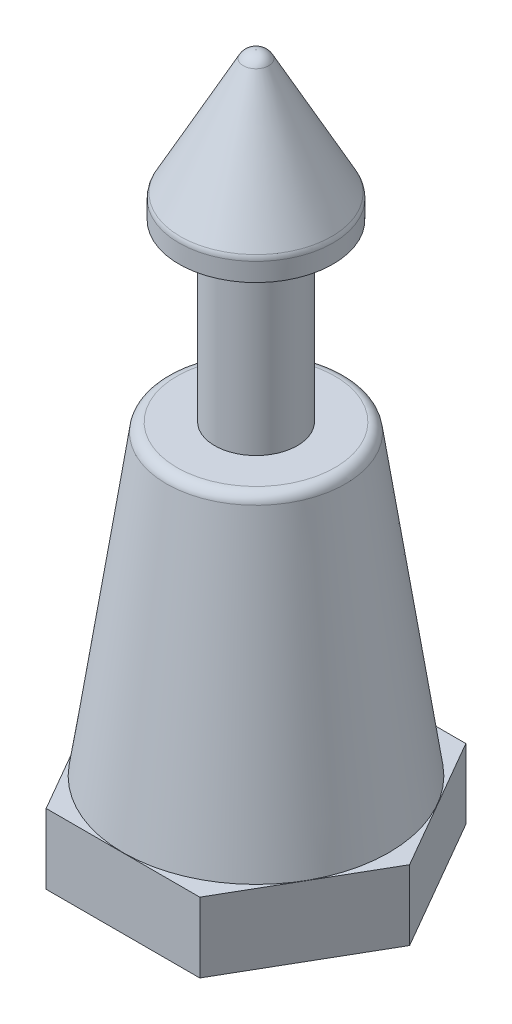
SolidWorks part; units mm, degrees
ref_plane "Front Plane" through (0, 0, 0) normal (0, 0, 1) x (1, 0, 0)
ref_plane "Top Plane" through (0, 0, 0) normal (0, 1, 0) x (1, 0, 0)
ref_plane "Right Plane" through (0, 0, 0) normal (1, 0, 0) x (0, 0, -1)
sketch "Sketch1" plane through (0, 0, 0) normal (0, 0, 1) x (1, 0, 0)
  line L0 (0, 0) -> (0, 79.052) construction
  line L1 (4.826, 2.4892) -> (4.826, 0)
  line L3 (0, 0) -> (4.826, 0)
  line L4 (4.826, 2.4892) -> (3.2004, 13.6652)
  line L5 (3.2004, 13.6652) -> (1.4986, 13.6652)
  line L6 (1.4986, 13.6652) -> (1.4986, 20.0152)
  line L7 (1.4986, 20.0152) -> (2.794, 20.0152)
  line L8 (2.794, 20.0152) -> (2.794, 20.7772)
  line L9 (2.794, 20.7772) -> (0.3175, 25.3492)
  line L10 (0.3175, 25.3492) -> (0, 25.3492)
  line L11 (0, 25.3492) -> (0, 0)
  dimension "D1" = 9.652
  dimension "D2" = 2.4892
  dimension "D3" = 6.35
  dimension "D4" = 0.762
  dimension "D5" = 25.3492
  dimension "D6" = 5.588
  dimension "D7" = 0.635
  dimension "D8" = 2.9972
  dimension "D9" = 13.6652
  dimension "D10" = 6.4008
revolve "Revolve1" add sketch "Sketch1" angle 360 about L0
sketch "Sketch2" plane through (0, 0, 0) normal (0, -1, 0) x (1, 0, 0)
  line L0 (0, 0) -> (5.5726, 0) construction
  line L1 (5.5726, 0) -> (2.7863, 4.826)
  line L2 (2.7863, 4.826) -> (-2.7863, 4.826)
  line L3 (-2.7863, 4.826) -> (-5.5726, 0)
  line L4 (-5.5726, 0) -> (-2.7863, -4.826)
  line L5 (-2.7863, -4.826) -> (2.7863, -4.826)
  line L6 (2.7863, -4.826) -> (5.5726, 0)
  circle A0 centre (0, 0) radius 4.826 construction
  dimension "D1" = 9.652
extrude "Boss-Extrude1" add sketch "Sketch2" against normal blind 2.54
sketch "Sketch3" plane through (0, 0, 0) normal (0, 0, 1) x (1, 0, 0)
  line L0 (1.4986, 13.6652) -> (1.4986, 20.0152) construction
  line L1 (1.4986, 13.6652) -> (1.4986, 20.0152)
  line L2 (1.4986, 20.0152) -> (3.0226, 20.0152)
  line L3 (1.4986, 13.6652) -> (3.0226, 13.6652)
  arc A0 (3.0226, 20.0152) -> (3.0226, 13.6652) centre (3.0226, 16.8402) cw
  dimension "D1" = 1.524
revolve "Revolve2-Mini_Post_Rubber_supress" [suppressed] add sketch "Sketch3" angle 360
fillet "Fillet1" radius 0.381 2 edges at (0, 13.6652, -3.2004) (0, 20.7772, -2.794)
fillet "Fillet2" radius 0.508 1 edges at (0, 25.3492, -0.3175)
sketch "Sketch4" plane through (0, 0, 0) normal (0, -1, 0) x (1, 0, 0)
  circle A0 centre (0, 0) radius 1.524
  dimension "D1" = 3.048
extrude "Cut-Extrude1" cut sketch "Sketch4" against normal blind 11.176
chamfer "Chamfer1" distance 0.762 angle 45 1 edges at (0, 0, -1.524)
